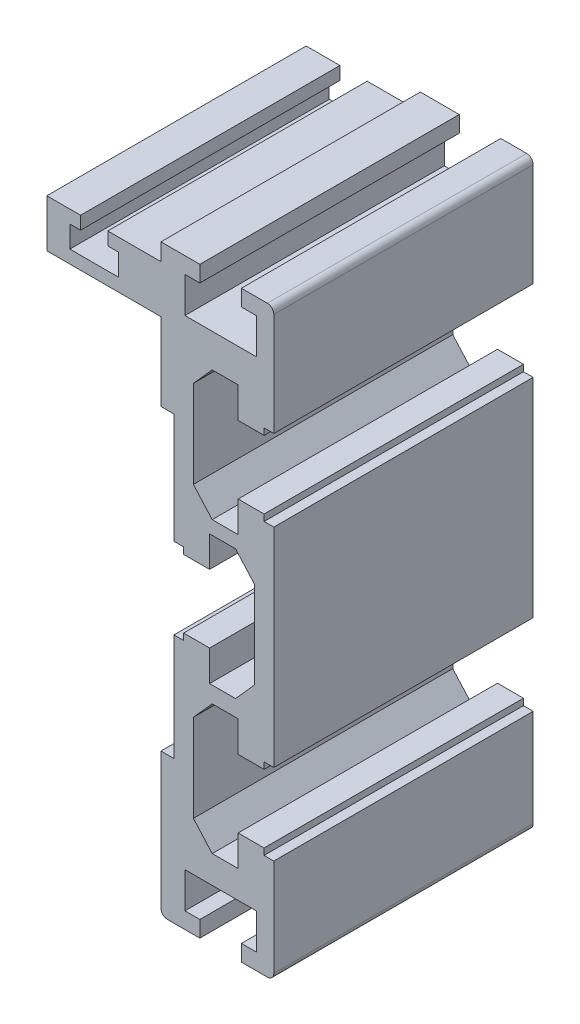
SolidWorks part; units mm, degrees
material "АД31Т ГОСТ 4784-97"
ref_plane "Спереди" through (0, 0, 0) normal (0, 0, 1) x (1, 0, 0)
ref_plane "Сверху" through (0, 0, 0) normal (0, 1, 0) x (1, 0, 0)
ref_plane "Справа" through (0, 0, 0) normal (1, 0, 0) x (0, 0, -1)
sketch "Model" plane through (0, 0, 0) normal (0, 0, 1) x (1, 0, 0)
  line L0 (-2.7, -8) -> (2.3, -8)
  line L1 (13.7, -7) -> (13.7, 8)
  line L2 (12.7, 82) -> (8.7, 82)
  line L3 (-21.3, 79.35) -> (-21.3, 72)
  line L4 (-21.3, 72) -> (-3.7, 72)
  line L5 (-3.7, 72) -> (-3.7, 60)
  line L6 (-21.3, 79.35) -> (-16.1, 79.35)
  line L7 (-3.7, 79.35) -> (-3.7, 82)
  line L8 (-3.7, 60) -> (-1.7, 60)
  line L9 (-1.7, 60) -> (-1.7, 43)
  line L10 (-1.7, 14) -> (-3.7, 14)
  line L11 (-3.7, 14) -> (-3.7, -7)
  line L12 (2.3, -5.5) -> (2.3, -8)
  line L13 (8.7, -5.5) -> (8.7, -8)
  line L14 (2.3, -5.5) -> (0, -5.5)
  line L15 (0, -5.5) -> (0, 0)
  line L16 (0, 0) -> (11, 0)
  line L17 (11, 0) -> (11, -5.5)
  line L18 (11, -5.5) -> (8.7, -5.5)
  line L19 (8.7, -8) -> (12.7, -8)
  line L20 (12.2, 9) -> (8.2, 9)
  line L21 (8.2, 9) -> (8.2, 4.25)
  line L22 (12.2, 19.5) -> (8.2, 19.5)
  line L23 (8.2, 19.5) -> (8.2, 24.25)
  line L24 (8.2, 24.25) -> (4.2, 24.25)
  line L25 (8.2, 4.25) -> (4.2, 4.25)
  line L26 (13.7, 20.5) -> (13.7, 52.6)
  line L27 (1.3, 21) -> (1.3, 7.5)
  line L28 (1.3, 21) -> (4.2, 24.25)
  line L29 (1.3, 7.5) -> (4.2, 4.25)
  line L30 (13.7, 20.5) -> (12.2, 20.5)
  line L31 (12.2, 20.5) -> (12.2, 19.5)
  line L32 (13.7, 8) -> (12.2, 8)
  line L33 (12.2, 8) -> (12.2, 9)
  line L34 (-0.2, 42) -> (3.8, 42)
  line L35 (3.8, 42) -> (3.8, 46.75)
  line L36 (-0.2, 31.5) -> (3.8, 31.5)
  line L37 (3.8, 31.5) -> (3.8, 26.75)
  line L38 (3.8, 26.75) -> (7.8, 26.75)
  line L39 (3.8, 46.75) -> (7.8, 46.75)
  line L40 (10.7, 30) -> (10.7, 43.5)
  line L41 (10.7, 30) -> (7.8, 26.75)
  line L42 (10.7, 43.5) -> (7.8, 46.75)
  line L43 (-1.7, 30.5) -> (-0.2, 30.5)
  line L44 (-0.2, 30.5) -> (-0.2, 31.5)
  line L45 (-1.7, 43) -> (-0.2, 43)
  line L46 (-0.2, 43) -> (-0.2, 42)
  line L47 (-1.7, 30.5) -> (-1.7, 14)
  line L48 (12.2, 53.6) -> (8.2, 53.6)
  line L49 (8.2, 53.6) -> (8.2, 48.85)
  line L50 (12.2, 64.1) -> (8.2, 64.1)
  line L51 (8.2, 64.1) -> (8.2, 68.85)
  line L52 (8.2, 68.85) -> (4.2, 68.85)
  line L53 (8.2, 48.85) -> (4.2, 48.85)
  line L54 (1.3, 65.6) -> (1.3, 52.1)
  line L55 (1.3, 65.6) -> (4.2, 68.85)
  line L56 (1.3, 52.1) -> (4.2, 48.85)
  line L57 (13.7, 65.1) -> (12.2, 65.1)
  line L58 (12.2, 65.1) -> (12.2, 64.1)
  line L59 (13.7, 52.6) -> (12.2, 52.6)
  line L60 (12.2, 52.6) -> (12.2, 53.6)
  line L61 (13.7, 65.1) -> (13.7, 81)
  line L62 (2.3, 79.5) -> (2.3, 82)
  line L63 (8.7, 79.5) -> (8.7, 82)
  line L64 (2.3, 79.5) -> (0, 79.5)
  line L65 (0, 79.5) -> (0, 74)
  line L66 (0, 74) -> (11, 74)
  line L67 (11, 74) -> (11, 79.5)
  line L68 (11, 79.5) -> (8.7, 79.5)
  line L69 (2.3, 82) -> (-3.7, 82)
  line L70 (-16.1, 79.35) -> (-16.1, 77.35)
  line L71 (-11.9, 79.35) -> (-11.9, 77.35)
  line L72 (-16.1, 77.35) -> (-17.75, 77.35)
  line L73 (-17.75, 77.35) -> (-17.75, 74)
  line L74 (-17.75, 74) -> (-10.25, 74)
  line L75 (-10.25, 74) -> (-10.25, 77.35)
  line L76 (-10.25, 77.35) -> (-11.9, 77.35)
  line L77 (-11.9, 79.35) -> (-3.7, 79.35)
  arc A0 (13.7, 81) -> (12.7, 82) centre (12.7, 81) ccw
  arc A1 (12.7, -8) -> (13.7, -7) centre (12.7, -7) ccw
  arc A2 (-3.7, -7) -> (-2.7, -8) centre (-2.7, -7) ccw
extrude "Бобышка-Вытянуть1" add sketch "Model" along normal blind 40
